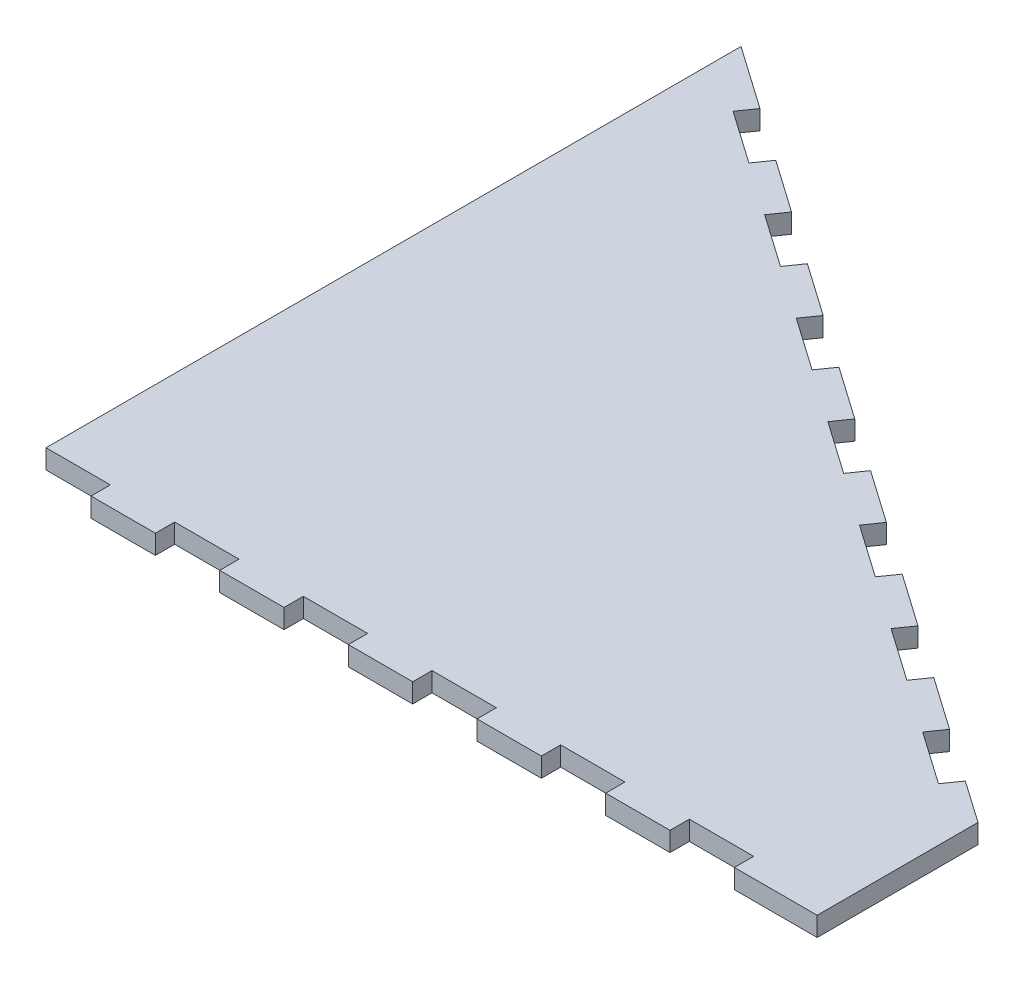
SolidWorks part; units mm, degrees
ref_plane "Plan de face" through (0, 0, 0) normal (0, 0, 1) x (1, 0, 0)
ref_plane "Plan de dessus" through (0, 0, 0) normal (0, 1, 0) x (1, 0, 0)
ref_plane "Plan de droite" through (0, 0, 0) normal (1, 0, 0) x (0, 0, -1)
sketch "Esquisse1" plane through (0, 0, 0) normal (0, 1, 0) x (1, 0, 0)
  line L0 (0, 0) -> (122.8728, 0) construction
  line L1 (0, 0) -> (0, 86.0365)
  line L2 (0, 86.0365) -> (122.8728, 0) construction
  line L3 (9.8298, 79.1535) -> (8.1091, 76.6961)
  line L4 (8.1091, 76.6961) -> (16.3006, 70.9603)
  line L5 (16.3006, 70.9603) -> (18.0213, 73.4178)
  line L6 (9.8298, 79.1535) -> (18.0213, 73.4178) construction
  line L7 (26.2129, 67.682) -> (34.4044, 61.9463) construction
  line L8 (32.6837, 59.4888) -> (34.4044, 61.9463)
  line L9 (24.4921, 65.2246) -> (32.6837, 59.4888)
  line L10 (26.2129, 67.682) -> (24.4921, 65.2246)
  line L11 (42.5959, 56.2105) -> (50.7874, 50.4747) construction
  line L12 (49.0667, 48.0173) -> (50.7874, 50.4747)
  line L13 (40.8752, 53.753) -> (49.0667, 48.0173)
  line L14 (42.5959, 56.2105) -> (40.8752, 53.753)
  line L15 (58.9789, 44.739) -> (67.1705, 39.0032) construction
  line L16 (65.4497, 36.5457) -> (67.1705, 39.0032)
  line L17 (57.2582, 42.2815) -> (65.4497, 36.5457)
  line L18 (58.9789, 44.739) -> (57.2582, 42.2815)
  line L19 (75.362, 33.2674) -> (83.5535, 27.5317) construction
  line L20 (81.8328, 25.0742) -> (83.5535, 27.5317)
  line L21 (73.6413, 30.81) -> (81.8328, 25.0742)
  line L22 (75.362, 33.2674) -> (73.6413, 30.81)
  line L23 (91.745, 21.7959) -> (99.9365, 16.0601) construction
  line L24 (98.2158, 13.6027) -> (99.9365, 16.0601)
  line L25 (90.0243, 19.3384) -> (98.2158, 13.6027)
  line L26 (91.745, 21.7959) -> (90.0243, 19.3384)
  line L27 (108.1281, 10.3244) -> (116.3196, 4.5886) construction
  line L28 (114.5989, 2.1312) -> (116.3196, 4.5886)
  line L29 (106.4073, 7.8669) -> (114.5989, 2.1312)
  line L30 (108.1281, 10.3244) -> (106.4073, 7.8669)
  line L31 (0, 86.0365) -> (9.8298, 79.1535)
  line L32 (0, 0) -> (122.8728, 0) construction
  line L33 (0, 0) -> (0, -22)
  line L34 (10, -25) -> (20, -25)
  line L35 (122.8728, 0) -> (122.8728, -25)
  line L36 (18.0213, 73.4178) -> (26.2129, 67.682)
  line L37 (34.4044, 61.9463) -> (42.5959, 56.2105)
  line L38 (50.7874, 50.4747) -> (58.9789, 44.739)
  line L39 (67.1705, 39.0032) -> (75.362, 33.2674)
  line L40 (83.5535, 27.5317) -> (91.745, 21.7959)
  line L41 (99.9365, 16.0601) -> (108.1281, 10.3244)
  line L42 (116.3196, 4.5886) -> (122.8728, 0)
  line L43 (20, -25) -> (20, -22)
  line L46 (0, -22) -> (10, -22)
  line L47 (10, -25) -> (10, -22)
  line L49 (30, -25) -> (30, -22)
  line L50 (20, -22) -> (30, -22)
  line L51 (40, -25) -> (40, -22)
  line L53 (50, -25) -> (50, -22)
  line L54 (40, -22) -> (50, -22)
  line L55 (60, -25) -> (60, -22)
  line L57 (70, -25) -> (70, -22)
  line L58 (60, -22) -> (70, -22)
  line L59 (80, -25) -> (80, -22)
  line L61 (90, -25) -> (90, -22)
  line L62 (80, -22) -> (90, -22)
  line L63 (100, -25) -> (100, -22)
  line L65 (110, -25) -> (110, -22)
  line L66 (100, -22) -> (110, -22)
  line L67 (30, -25) -> (40, -25)
  line L68 (50, -25) -> (60, -25)
  line L69 (70, -25) -> (80, -25)
  line L70 (90, -25) -> (100, -25)
  line L71 (110, -25) -> (122.8728, -25)
  dimension "D1" = 35
  dimension "D2" = 150
  dimension "D3" = 12
  dimension "D4" = 10
  dimension "D5" = 3
  dimension "D7" = 25
  dimension "D9" = 10
  dimension "D10" = 3
  dimension "D6" = 7
  dimension "D11" = 6
extrude "Boss.-Extru.1" add sketch "Esquisse1" along normal blind 3
